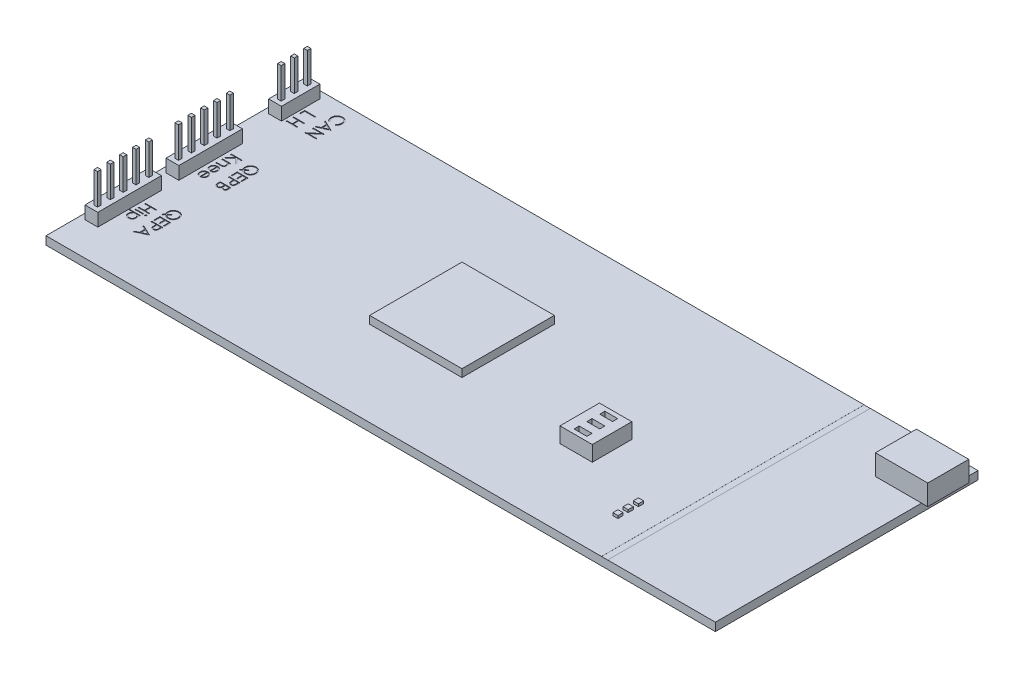
SolidWorks part; units mm, degrees
ref_plane "Ebene vorne" through (0, 0, 0) normal (0, 0, 1) x (1, 0, 0)
ref_plane "Ebene oben" through (0, 0, 0) normal (0, 1, 0) x (1, 0, 0)
ref_plane "Ebene rechts" through (0, 0, 0) normal (1, 0, 0) x (0, 0, -1)
sketch "Skizze1" plane through (0, 0, 0) normal (0, 1, 0) x (1, 0, 0)
  line L1 (-65.25, -25.6) -> (65.25, -25.6)
  line L2 (-65.25, -25.6) -> (-65.25, 25.6)
  line L3 (-65.25, 25.6) -> (65.25, 25.6)
  line L4 (65.25, -25.6) -> (65.25, 25.6)
  line L5 (-65.25, -25.6) -> (65.25, 25.6) construction
  line L6 (-65.25, 25.6) -> (65.25, -25.6) construction
  point P0 (0, 0)
  dimension "D1" = 51.2
  dimension "D2" = 130.5
extrude "Aufsatz-Linear austragen1" add sketch "Skizze1" along normal blind 1.6
sketch "Skizze2" plane through (65.25, 0, 0) normal (1, 0, 0) x (0, 0, -1)
  line L0 (-25.6, 1.6) -> (25.6, 1.6) construction
  line L1 (14.6, 1.6) -> (22.6, 1.6)
  line L2 (14.6, 1.6) -> (14.6, 5.6)
  line L3 (14.6, 5.6) -> (22.6, 5.6)
  line L4 (22.6, 1.6) -> (22.6, 5.6)
  line L5 (25.6, 1.6) -> (25.6, 0) construction
  dimension "D1" = 8
  dimension "D2" = 4
  dimension "D3" = 3
extrude "Aufsatz-Linear austragen2" add sketch "Skizze2" along normal blind 1.2 and the other way blind 9
sketch "Skizze4" plane through (0, 1.6, 0) normal (0, 1, 0) x (1, 0, 0)
  line L0 (65.25, 25.6) -> (-65.25, 25.6) construction
  line L1 (-64.15, 24.2) -> (-61.65, 24.2)
  line L2 (-64.15, 24.2) -> (-64.15, 16.7)
  line L3 (-64.15, 16.7) -> (-61.65, 16.7)
  line L4 (-61.65, 24.2) -> (-61.65, 16.7)
  line L5 (-64.15, 9.1) -> (-61.65, 9.1)
  line L6 (-64.15, 9.1) -> (-64.15, -3.3)
  line L7 (-64.15, -3.3) -> (-61.65, -3.3)
  line L8 (-61.65, 9.1) -> (-61.65, -3.3)
  line L9 (-64.15, -6.7) -> (-61.65, -6.7)
  line L10 (-64.15, -6.7) -> (-64.15, -19.1)
  line L11 (-64.15, -19.1) -> (-61.65, -19.1)
  line L12 (-61.65, -6.7) -> (-61.65, -19.1)
  line L13 (-65.25, 25.6) -> (-65.25, -25.6) construction
  dimension "D1" = 2.5
  dimension "D2" = 7.5
  dimension "D3" = 1.4
  dimension "D4" = 1.1
  dimension "D5" = 16.5
  dimension "D6" = 32.3
  dimension "D7" = 12.4
extrude "Aufsatz-Linear austragen3" add sketch "Skizze4" along normal blind 2.5
sketch "Skizze5" plane through (0, 4.1, 0) normal (0, 1, 0) x (1, 0, 0)
  line L0 (-62.9, 29.2916) -> (-62.9, -22.1565) construction
  line L1 (-64.15, 24.2) -> (-64.15, 16.7) construction
  line L2 (-61.65, 16.7) -> (-61.65, 24.2) construction
  line L3 (-66.6105, 20.45) -> (-60.666, 20.45) construction
  line L4 (-63.25, 23.35) -> (-62.55, 23.35)
  line L5 (-63.25, 23.35) -> (-63.25, 22.65)
  line L6 (-63.25, 22.65) -> (-62.55, 22.65)
  line L7 (-62.55, 23.35) -> (-62.55, 22.65)
  line L8 (-63.25, 20.8) -> (-62.55, 20.8)
  line L9 (-63.25, 20.8) -> (-63.25, 20.1)
  line L10 (-63.25, 20.1) -> (-62.55, 20.1)
  line L11 (-62.55, 20.8) -> (-62.55, 20.1)
  line L12 (-63.25, 18.25) -> (-62.55, 18.25)
  line L13 (-63.25, 18.25) -> (-63.25, 17.55)
  line L14 (-63.25, 17.55) -> (-62.55, 17.55)
  line L15 (-62.55, 18.25) -> (-62.55, 17.55)
  line L16 (-61.65, 24.2) -> (-64.15, 24.2) construction
  line L17 (-64.15, 16.7) -> (-61.65, 16.7) construction
  line L18 (-68.1087, 2.9) -> (-59.7938, 2.9) construction
  line L19 (-63.25, 8.25) -> (-62.55, 8.25)
  line L20 (-63.25, 8.25) -> (-63.25, 7.55)
  line L21 (-63.25, 7.55) -> (-62.55, 7.55)
  line L22 (-62.55, 8.25) -> (-62.55, 7.55)
  line L23 (-63.25, 5.75) -> (-62.55, 5.75)
  line L24 (-63.25, 5.75) -> (-63.25, 5.05)
  line L25 (-63.25, 5.05) -> (-62.55, 5.05)
  line L26 (-62.55, 5.75) -> (-62.55, 5.05)
  line L27 (-63.25, 3.25) -> (-62.55, 3.25)
  line L28 (-63.25, 3.25) -> (-63.25, 2.55)
  line L29 (-63.25, 2.55) -> (-62.55, 2.55)
  line L30 (-62.55, 3.25) -> (-62.55, 2.55)
  line L31 (-63.25, 0.75) -> (-62.55, 0.75)
  line L32 (-63.25, 0.75) -> (-63.25, 0.05)
  line L33 (-63.25, 0.05) -> (-62.55, 0.05)
  line L34 (-62.55, 0.75) -> (-62.55, 0.05)
  line L35 (-63.25, -1.75) -> (-62.55, -1.75)
  line L36 (-63.25, -1.75) -> (-63.25, -2.45)
  line L37 (-63.25, -2.45) -> (-62.55, -2.45)
  line L38 (-62.55, -1.75) -> (-62.55, -2.45)
  line L39 (-63.25, -7.55) -> (-62.55, -7.55)
  line L40 (-63.25, -7.55) -> (-63.25, -8.25)
  line L41 (-63.25, -8.25) -> (-62.55, -8.25)
  line L42 (-62.55, -7.55) -> (-62.55, -8.25)
  line L43 (-63.25, -10.05) -> (-62.55, -10.05)
  line L44 (-63.25, -10.05) -> (-63.25, -10.75)
  line L45 (-63.25, -10.75) -> (-62.55, -10.75)
  line L46 (-62.55, -10.05) -> (-62.55, -10.75)
  line L47 (-63.25, -12.55) -> (-62.55, -12.55)
  line L48 (-63.25, -12.55) -> (-63.25, -13.25)
  line L49 (-63.25, -13.25) -> (-62.55, -13.25)
  line L50 (-62.55, -12.55) -> (-62.55, -13.25)
  line L51 (-63.25, -15.05) -> (-62.55, -15.05)
  line L52 (-63.25, -15.05) -> (-63.25, -15.75)
  line L53 (-63.25, -15.75) -> (-62.55, -15.75)
  line L54 (-62.55, -15.05) -> (-62.55, -15.75)
  line L55 (-63.25, -17.55) -> (-62.55, -17.55)
  line L56 (-63.25, -17.55) -> (-63.25, -18.25)
  line L57 (-63.25, -18.25) -> (-62.55, -18.25)
  line L58 (-62.55, -17.55) -> (-62.55, -18.25)
  line L59 (-61.65, 9.1) -> (-64.15, 9.1) construction
  line L60 (-64.15, -3.3) -> (-61.65, -3.3) construction
  line L61 (-67.6279, -12.9) -> (-60.666, -12.9) construction
  line L62 (-61.65, -6.7) -> (-64.15, -6.7) construction
  line L63 (-64.15, -19.1) -> (-61.65, -19.1) construction
  dimension "D1" = 0.7
  dimension "D2" = 4.4
  dimension "D3" = 5.7
  dimension "D4" = 10.7
  dimension "D5" = 5.7
  dimension "D6" = 10.7
extrude "Aufsatz-Linear austragen4" add sketch "Skizze5" along normal blind 6
sketch "Skizze6" plane through (0, 1.6, 0) normal (0, 1, 0) x (1, 0, 0)
  line L0 (65.25, 25.6) -> (-65.25, 25.6) construction
  line L1 (43.05, 25.6) -> (44.25, 25.6)
  line L2 (43.05, 25.6) -> (43.05, -25.6)
  line L3 (43.05, -25.6) -> (44.25, -25.6)
  line L4 (44.25, 25.6) -> (44.25, -25.6)
  line L5 (-65.25, -25.6) -> (65.25, -25.6) construction
  line L6 (65.25, -25.6) -> (65.25, 14.6) construction
  dimension "D1" = 1.2
  dimension "D2" = 21
extrude "Schnitt-Linear austragen1" cut sketch "Skizze6" against normal blind 0.01
sketch "Skizze7" plane through (0, 1.6, 0) normal (0, 1, 0) x (1, 0, 0)
  line L0 (-73.4444, 0) -> (19.4459, 0) construction
  line L1 (-18.75, -9) -> (-0.75, -9)
  line L2 (-18.75, -9) -> (-18.75, 9)
  line L3 (-18.75, 9) -> (-0.75, 9)
  line L4 (-0.75, -9) -> (-0.75, 9)
  line L5 (-18.75, -9) -> (-0.75, 9) construction
  line L6 (-18.75, 9) -> (-0.75, -9) construction
  line L7 (65.25, -25.6) -> (65.25, 14.6) construction
  point P0 (-9.75, 0)
  dimension "D1" = 18
  dimension "D2" = 66
extrude "Aufsatz-Linear austragen5" add sketch "Skizze7" along normal blind 1.5
sketch "Skizze8" plane through (0, 1.6, 0) normal (0, 1, 0) x (1, 0, 0)
  line L0 (65.25, -25.6) -> (65.25, 14.6) construction
  line L1 (19.95, -2.9) -> (26.25, -2.9)
  line L2 (19.95, -2.9) -> (19.95, -10.6)
  line L3 (19.95, -10.6) -> (26.25, -10.6)
  line L4 (26.25, -2.9) -> (26.25, -10.6)
  line L5 (19.95, -2.9) -> (26.25, -10.6) construction
  line L6 (19.95, -10.6) -> (26.25, -2.9) construction
  line L7 (-65.25, -25.6) -> (43.05, -25.6) construction
  point P0 (23.1, -6.75)
  dimension "D1" = 7.7
  dimension "D2" = 6.3
  dimension "D3" = 39
  dimension "D4" = 15
extrude "Aufsatz-Linear austragen6" add sketch "Skizze8" along normal blind 3
sketch "Skizze9" plane through (0, 4.6, 0) normal (0, 1, 0) x (1, 0, 0)
  line L0 (17.552, -6.75) -> (26.77, -6.75) construction
  line L1 (21.85, -3.75) -> (24.35, -3.75)
  line L2 (21.85, -3.75) -> (21.85, -4.75)
  line L3 (21.85, -4.75) -> (24.35, -4.75)
  line L4 (24.35, -3.75) -> (24.35, -4.75)
  line L5 (21.85, -6.25) -> (24.35, -6.25)
  line L6 (21.85, -6.25) -> (21.85, -7.25)
  line L7 (21.85, -7.25) -> (24.35, -7.25)
  line L8 (24.35, -6.25) -> (24.35, -7.25)
  line L9 (21.85, -8.75) -> (24.35, -8.75)
  line L10 (21.85, -8.75) -> (21.85, -9.75)
  line L11 (21.85, -9.75) -> (24.35, -9.75)
  line L12 (24.35, -8.75) -> (24.35, -9.75)
  line L13 (26.25, -2.9) -> (19.95, -2.9) construction
  line L14 (19.95, -10.6) -> (26.25, -10.6) construction
  line L15 (23.1, -1.7044) -> (23.1, -10.9665) construction
  line L16 (19.95, -2.9) -> (19.95, -10.6) construction
  line L17 (26.25, -10.6) -> (26.25, -2.9) construction
  dimension "D1" = 2.5
  dimension "D2" = 1
  dimension "D3" = 4
extrude "Schnitt-Linear austragen2" cut sketch "Skizze9" against normal blind 1
sketch "Skizze10" plane through (0, 1.6, 0) normal (0, 1, 0) x (1, 0, 0)
  line L0 (21.5527, -15.1) -> (30.3375, -15.1) construction
  line L1 (37.25, -12.6) -> (38.25, -12.6)
  line L2 (37.25, -12.6) -> (37.25, -13.6)
  line L3 (37.25, -13.6) -> (38.25, -13.6)
  line L4 (38.25, -12.6) -> (38.25, -13.6)
  line L5 (37.25, -14.6) -> (38.25, -14.6)
  line L6 (37.25, -14.6) -> (37.25, -15.6)
  line L7 (37.25, -15.6) -> (38.25, -15.6)
  line L8 (38.25, -14.6) -> (38.25, -15.6)
  line L9 (37.25, -16.6) -> (38.25, -16.6)
  line L10 (37.25, -16.6) -> (37.25, -17.6)
  line L11 (37.25, -17.6) -> (38.25, -17.6)
  line L12 (38.25, -16.6) -> (38.25, -17.6)
  line L13 (65.25, -25.6) -> (65.25, 14.6) construction
  line L14 (-65.25, -25.6) -> (43.05, -25.6) construction
  dimension "D1" = 1
  dimension "D2" = 5
  dimension "D3" = 27
  dimension "D4" = 8
extrude "Aufsatz-Linear austragen7" add sketch "Skizze10" along normal blind 0.5
sketch "Skizze11" plane through (0, 1.6, 0) normal (0, 1, 0) x (1, 0, 0)
  line L0 (-57.3727, 7.5435) -> (-57.3727, -1.8093) construction
  line L1 (-57.3727, -8.2357) -> (-57.3727, -16.7218) construction
  line L2 (-57.3727, 23.4774) -> (-57.3727, 17.0069) construction
  text T0 "QEPB\r\nKnee" font "Century Gothic" height in points 8
  text T1 "QEPA\r\nHip" font "Century Gothic" height in points 8
  text T2 "CAN\r\n   L H" font "Century Gothic" height 2.1167
extrude "Schnitt-Linear austragen3" cut sketch "Skizze11" against normal blind 0.1
